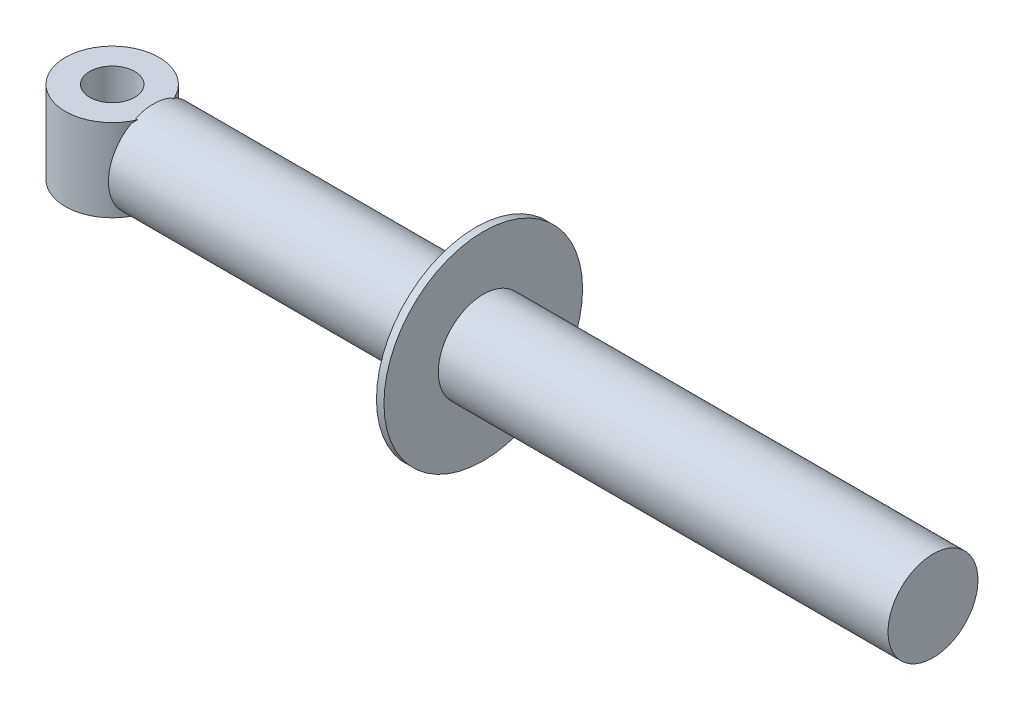
SolidWorks part; units mm, degrees
material "AISI 316 Stainless Steel Sheet (SS)"
ref_plane "Front Plane" through (0, 0, 0) normal (0, 0, 1) x (1, 0, 0)
ref_plane "Top Plane" through (0, 0, 0) normal (0, 1, 0) x (1, 0, 0)
ref_plane "Right Plane" through (0, 0, 0) normal (1, 0, 0) x (0, 0, -1)
sketch "Sketch1" plane through (0, 0, 0) normal (0, 1, 0) x (1, 0, 0)
  line L0 (0, 0) -> (0, 26.5)
  line L1 (0, 26.5) -> (2, 26.5)
  line L3 (2, 12) -> (122, 12)
  line L4 (122, 12) -> (122, 0)
  line L5 (122, 0) -> (0, 0)
  line L7 (2, 26.5) -> (2, 12)
  point P3 (0, 0)
  point P4 (0, 0)
  point P9 (0, 0)
  point P11 (0, 0)
  point P12 (0, 0)
  dimension "D1" = 26.5
  dimension "D2" = 120
  dimension "D4" = 12
  dimension "D6" = 2
revolve "Revolve1" add sketch "Sketch1" angle 360 about L5
sketch "Sketch2" plane through (0, 0, 0) normal (-1, 0, 0) x (0, 0, 1)
  circle A0 centre (0, 0) radius 12
  dimension "D1" = 24
extrude "Boss-Extrude1" add sketch "Sketch2" along normal blind 86
sketch "Sketch3" plane through (0, 0, 0) normal (0, 1, 0) x (1, 0, 0)
  line L4 (-86, 12) -> (-86, -12) construction
  circle A0 centre (-97, 0) radius 12.5
  circle A1 centre (-97, 0) radius 6
  point P7 (0, 0)
  dimension "D1" = 12
  dimension "D2" = 25
  dimension "D3" = 11
extrude "Boss-Extrude2" add sketch "Sketch3" along normal mid plane 22
